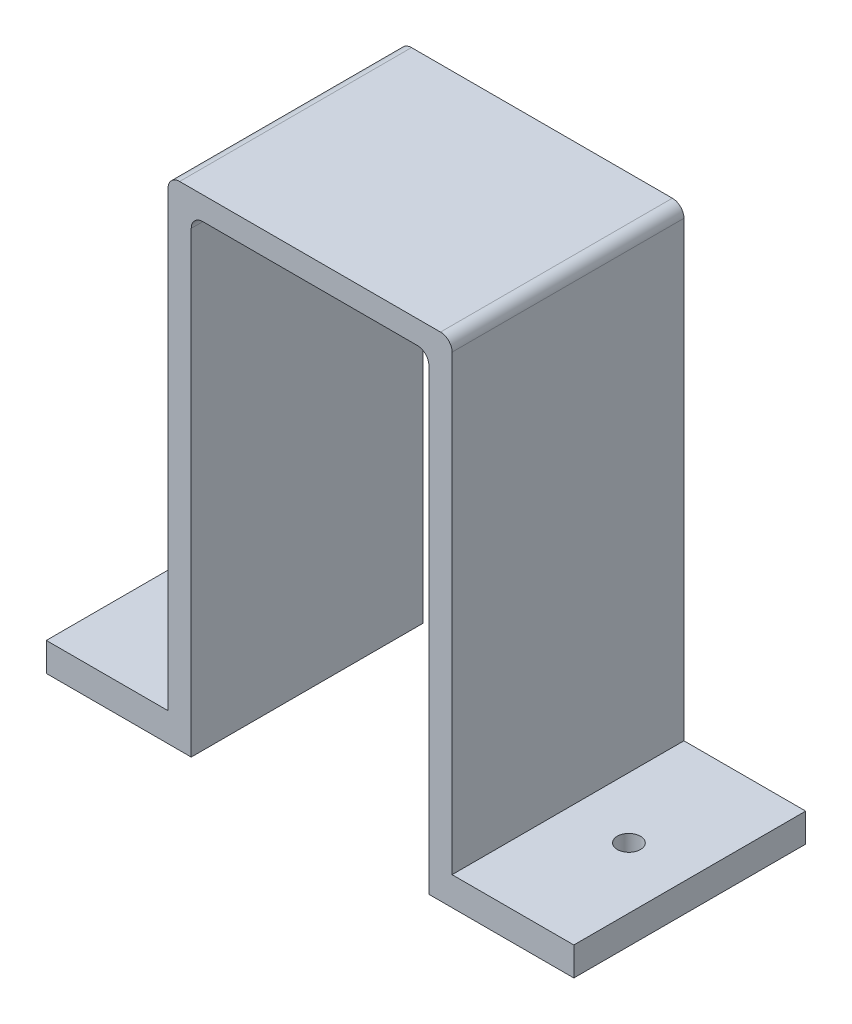
SolidWorks part; units mm, degrees
ref_plane "Front Plane" through (0, 0, 0) normal (0, 0, 1) x (1, 0, 0)
ref_plane "Top Plane" through (0, 0, 0) normal (0, 1, 0) x (1, 0, 0)
ref_plane "Right Plane" through (0, 0, 0) normal (1, 0, 0) x (0, 0, -1)
sketch "Sketch1" plane through (0, 0, 0) normal (0, 0, 1) x (1, 0, 0)
  line L0 (-22.5, -10.2652) -> (-22.5, 30.2348)
  line L1 (-22.5, 30.2348) -> (-2, 30.2348)
  line L2 (-2, 30.2348) -> (-2, -10.2652)
  line L3 (-22.5, -10.2652) -> (-26.0679, -10.2652)
  line L4 (-24.5, -7.7971) -> (-24.5, 32.2348)
  line L5 (-24.5, 32.2348) -> (0, 32.2348)
  line L6 (0, 32.2348) -> (0, -7.7971)
  line L7 (0, -10.2652) -> (-2, -10.2652)
  line L8 (-26.0679, -10.2652) -> (-35, -10.2652)
  line L9 (-35, -10.2652) -> (-35, -7.7971)
  line L10 (-35, -7.7971) -> (-24.5, -7.7971)
  line L11 (0, -10.2652) -> (10.5, -10.2652)
  line L12 (10.5, -10.2652) -> (10.5, -7.7971)
  line L13 (10.5, -7.7971) -> (0, -7.7971)
  dimension "D1" = 20.5
  dimension "D2" = 40.5
  dimension "D3" = 40.5
  dimension "D4" = 2
  dimension "D5" = 2
  dimension "D6" = 2
  dimension "D7" = 12.5
  dimension "D8" = 12.5
extrude "Boss-Extrude1" add sketch "Sketch1" along normal blind 20 contours L8 L9 L10 L4 L5 L6 L13 L12 L11 L7 L2 L1 L0 L3
fillet "Fillet1" radius 1 4 edges at (0, 32.2348, 10) (-24.5, 32.2348, 10) (-2, 30.2348, 10) (-22.5, 30.2348, 10)
sketch "Sketch2" plane through (0, -7.7971, 0) normal (0, 1, 0) x (1, 0, 0)
  line L0 (10.5, 0) -> (0, 0) construction
  line L1 (-35, -20) -> (-35, 0) construction
  line L3 (-35, 0) -> (-24.5, 0) construction
  circle A0 centre (-29.75, -10) radius 1
  circle A1 centre (5.25, -10) radius 1
  point P6 (5.25, 0)
  dimension "D1" = 2
  dimension "D2" = 2
  dimension "D3" = 5.25
  dimension "D4" = 10
  dimension "D5" = 10
extrude "Cut-Extrude1" cut sketch "Sketch2" against normal blind 20
